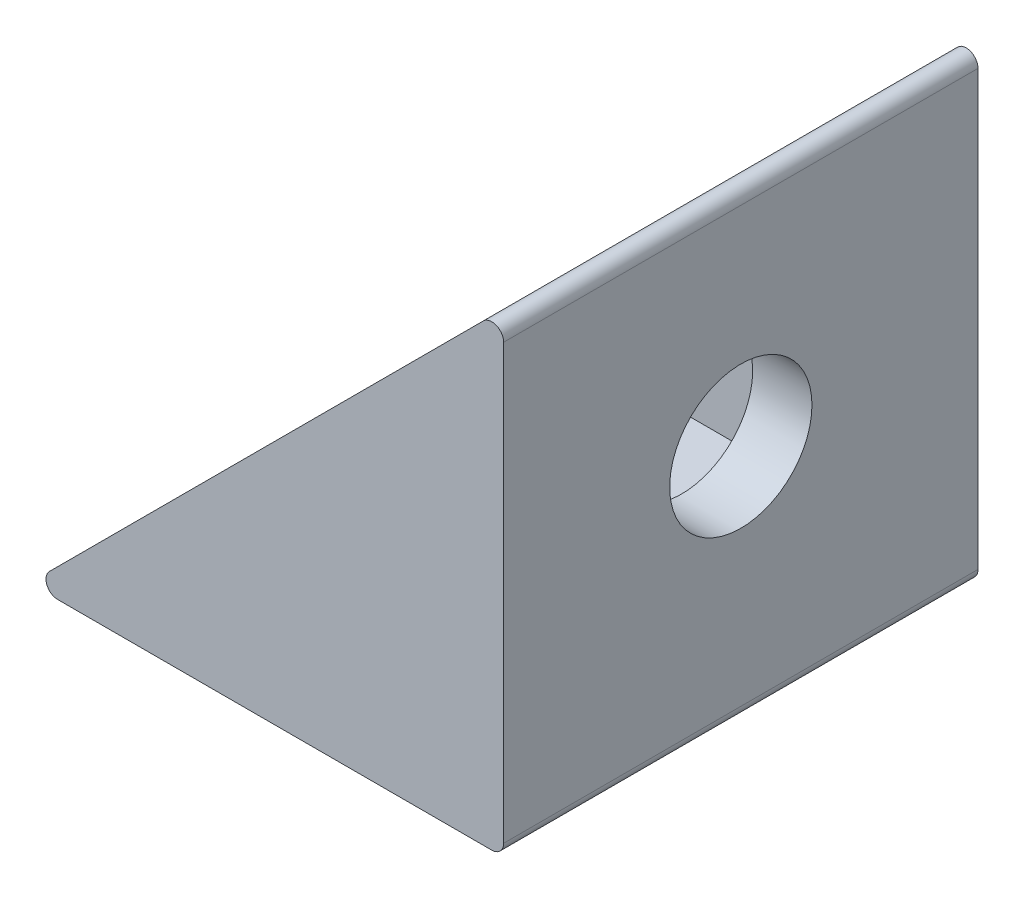
SolidWorks part; units mm, degrees
material "1060 Alloy"
ref_plane "Front Plane" through (0, 0, 0) normal (0, 0, 1) x (1, 0, 0)
ref_plane "Top Plane" through (0, 0, 0) normal (0, 1, 0) x (1, 0, 0)
ref_plane "Right Plane" through (0, 0, 0) normal (1, 0, 0) x (0, 0, -1)
sketch "Sketch1" plane through (0, 0, 0) normal (0, 1, 0) x (1, 0, 0)
  line L1 (-10, 10) -> (10, 10)
  line L2 (-10, 10) -> (-10, -10)
  line L3 (-10, -10) -> (10, -10)
  line L4 (10, 10) -> (10, -10)
  line L5 (-10, 10) -> (10, -10) construction
  line L6 (-10, -10) -> (10, 10) construction
  point P0 (0, 0)
  dimension "D1" = 20
  dimension "D2" = 20
extrude "Boss-Extrude1" add sketch "Sketch1" along normal blind 20
sketch "Sketch2" plane through (0, 0, 10) normal (0, 0, 1) x (1, 0, 0)
  line L0 (-10, 0) -> (10, 20)
  line L1 (10, 20) -> (-10, 20)
  line L2 (-10, 20) -> (-10, 0)
extrude "Cut-Extrude1" cut sketch "Sketch2" against normal through all both and the other way through all
sketch "Sketch3" plane through (10, 0, 0) normal (1, 0, 0) x (0, 0, -1)
  line L0 (-10, 10) -> (10, 10) construction
  line L1 (-10, 20) -> (-10, 0) construction
  line L2 (10, 20) -> (10, 0) construction
  circle A0 centre (0, 10) radius 3
  dimension "D1" = 6
extrude "Cut-Extrude2" cut sketch "Sketch3" against normal through all contours A0
sketch "Sketch4" plane through (0, 0, 0) normal (0, -1, 0) x (1, 0, 0)
  circle A0 centre (0, 0) radius 3
  dimension "D1" = 6
extrude "Cut-Extrude3" cut sketch "Sketch4" against normal through all
ref_plane "Plane1" through (0, 20, 0) normal (0, 1, 0) x (1, 0, 0)
sketch "Sketch5" plane through (0, 20, 0) normal (0, 1, 0) x (1, 0, 0)
  line L1 (-7.5, -7.5) -> (7.5, -7.5)
  line L2 (-7.5, -7.5) -> (-7.5, 7.5)
  line L3 (-7.5, 7.5) -> (7.5, 7.5)
  line L4 (7.5, -7.5) -> (7.5, 7.5)
  line L5 (-7.5, -7.5) -> (7.5, 7.5) construction
  line L6 (-7.5, 7.5) -> (7.5, -7.5) construction
  point P0 (0, 0)
  dimension "D1" = 15
extrude "Cut-Extrude5" cut sketch "Sketch5" against normal offset from surface (17.5 mm away) 2.5 up to face at (0, 0, -3)
fillet "Fillet1" radius 0.5 3 edges at (10, 0, 0) (10, 20, 0) (-10, 0, 0)
